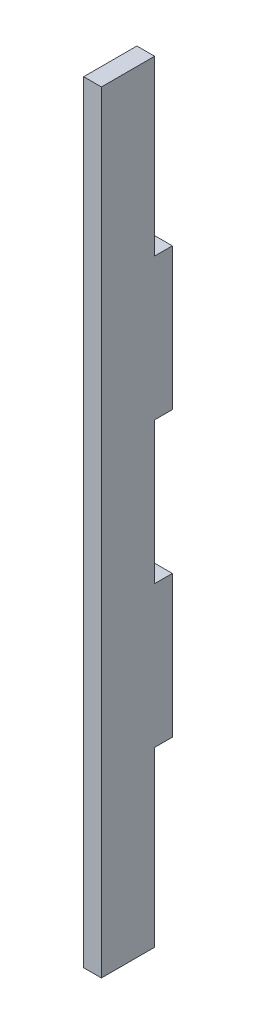
SolidWorks part; units mm, degrees
material "Acrylic (Medium-high impact)"
ref_plane "Front" through (0, 0, 0) normal (0, 0, 1) x (1, 0, 0)
ref_plane "Top" through (0, 0, 0) normal (0, 1, 0) x (1, 0, 0)
ref_plane "Right" through (0, 0, 0) normal (1, 0, 0) x (0, 0, -1)
sketch "Sketch1" plane through (0, 0, 0) normal (1, 0, 0) x (0, 0, -1)
  line L3 (-6.35, -132.588) -> (6.35, -132.588)
  line L69 (6.35, 0) -> (6.35, -132.588)
  line L70 (-6.35, -132.588) -> (-6.35, 0)
  line L71 (-6.35, -127) -> (6.35, -127) construction
  line L74 (4.7625, -25.4) -> (4.7625, -50.8) construction
  line L75 (4.7625, -76.2) -> (4.7625, -101.6) construction
  line L82 (6.35, 0) -> (-6.35, 0)
  line L83 (6.35, 0) -> (6.35, -25.4)
  line L84 (6.35, 0) -> (3.175, 0)
  line L85 (3.175, 0) -> (3.175, -25.4)
  line L86 (6.35, -25.4) -> (3.175, -25.4)
  line L87 (6.35, -50.8) -> (6.35, -76.2)
  line L88 (6.35, -50.8) -> (3.175, -50.8)
  line L89 (3.175, -50.8) -> (3.175, -76.2)
  line L90 (6.35, -76.2) -> (3.175, -76.2)
  line L96 (6.35, -101.6) -> (3.175, -101.6)
  line L97 (6.35, -101.6) -> (6.35, -127)
  line L98 (6.35, -127) -> (3.175, -127)
  line L99 (3.175, -101.6) -> (3.175, -127)
  line L101 (6.35, -127) -> (3.175, -127)
  line L102 (6.35, -127) -> (6.35, -132.588)
  line L103 (6.35, -132.588) -> (3.175, -132.588)
  line L104 (3.175, -127) -> (3.175, -132.588)
  line L106 (-6.35, 0) -> (3.175, 0)
  line L107 (-6.35, 0) -> (-6.35, 5.588)
  line L108 (-6.35, 5.588) -> (3.175, 5.588)
  line L109 (3.175, 0) -> (3.175, 5.588)
  point P4 (0, -132.588)
  dimension "D2" = 25.4
  dimension "D4" = 3.175
  dimension "D1" = 25.4
  dimension "D5" = 9.525
  dimension "D3" = 5.588
extrude "Boss-Extrude1" add sketch "Sketch1" along normal blind 3.175
sketch "Sketch2" [suppressed] plane through (3.175, 0, 0) normal (1, 0, 0) x (0, 0, -1)
  line L6 (6.35, -70.0024) -> (18.542, -70.0024)
  line L7 (6.35, -70.0024) -> (6.35, -85.9536)
  line L8 (6.35, -85.9536) -> (18.542, -85.9536)
  line L9 (18.542, -70.0024) -> (18.542, -85.9536)
  line L11 (6.35, -76.3905) -> (12.192, -76.3905)
  line L12 (6.35, -76.3905) -> (6.35, -79.5655)
  line L13 (6.35, -79.5655) -> (12.192, -79.5655)
  line L14 (12.192, -76.3905) -> (12.192, -79.5655)
  line L31 (6.35, -70.0024) -> (3.175, -70.0024) construction
  point P22 (12.192, -77.978)
  point P27 (18.542, -77.978)
  dimension "D1" = 12.192
  dimension "D3" = 3.175
  dimension "D4" = 5.842
extrude "Boss-Extrude2" [suppressed] add sketch "Sketch2" against normal up to surface (2.9972 mm away)
equation "\"bottomThickness\"= .220in"
equation "\"wallThickness\"= .125in"
equation "\"D4@Sketch1\"=\"wallThickness\""
equation "\"D1@Boss-Extrude1\"=\"wallThickness\""
equation "\"D3@Sketch1\"=\"bottomThickness\""
